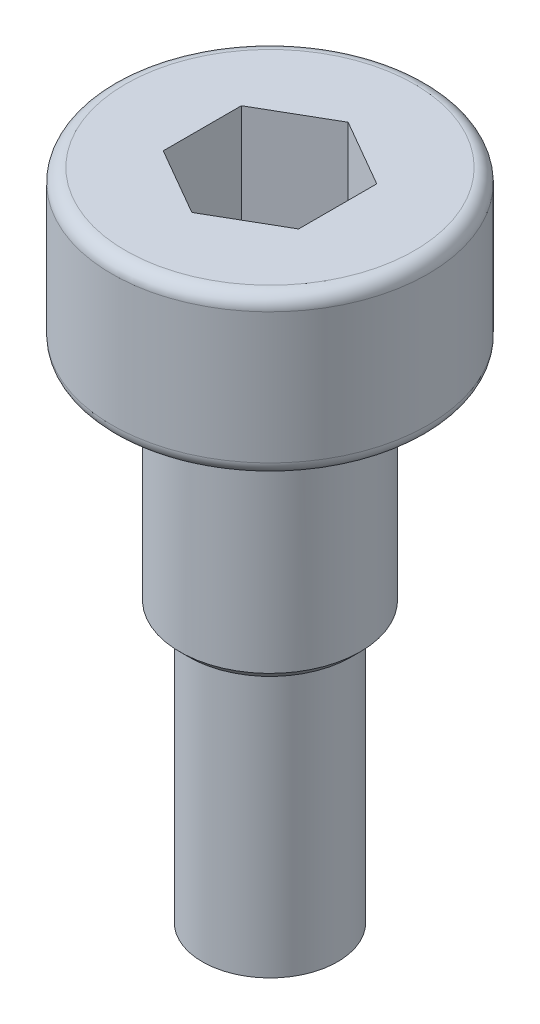
SolidWorks part; units mm, degrees
ref_plane "Front Plane" through (0, 0, 0) normal (0, 0, 1) x (1, 0, 0)
ref_plane "Top Plane" through (0, 0, 0) normal (0, 1, 0) x (1, 0, 0)
ref_plane "Right Plane" through (0, 0, 0) normal (1, 0, 0) x (0, 0, -1)
sketch "Sketch1" plane through (0, 0, 0) normal (0, 0, 1) x (1, 0, 0)
  line L0 (0, 0) -> (0, -29.1917) construction
  line L1 (0, 3.5) -> (-3.5, 3.5)
  line L2 (-3.5, 3.5) -> (-3.5, 0)
  line L3 (-3.5, 0) -> (-2, 0)
  line L4 (-2, 0) -> (-2, -5)
  line L5 (-2, -5) -> (-1.5, -5)
  line L6 (-1.5, -5) -> (-1.5, -11)
  line L7 (-1.5, -11) -> (0, -11)
  line L8 (0, 0) -> (0, 8.6899) construction
  line L9 (0, 3.5) -> (0, -11)
  dimension "D1" = 4
  dimension "D2" = 3
  dimension "D3" = 6
  dimension "D4" = 7
  dimension "D5" = 3.5
  dimension "D6" = 5
revolve "Revolve1" add sketch "Sketch1" angle 360 about L9
cosmetic thread "Cosmetic Thread1" parameters "D2"=2.459
fillet "Fillet1" radius 0.3 2 edges at (-3.5, 0, 0) (-3.5, 3.5, 0)
sketch "Sketch2" plane through (0, 3.5, 0) normal (0, 1, 0) x (1, 0, 0)
  line L1 (1.5, 0.866) -> (0, 1.7321)
  line L2 (0, 1.7321) -> (-1.5, 0.866)
  line L3 (-1.5, 0.866) -> (-1.5, -0.866)
  line L4 (-1.5, -0.866) -> (0, -1.7321)
  line L5 (0, -1.7321) -> (1.5, -0.866)
  line L6 (1.5, -0.866) -> (1.5, 0.866)
  circle A0 centre (0, 0) radius 1.5 construction
  dimension "D1" = 3
extrude "Cut-Extrude1" cut sketch "Sketch2" against normal blind 2.4
chamfer "Chamfer1" distance 0.2 angle 45 1 edges at (-2, -5, 0)
